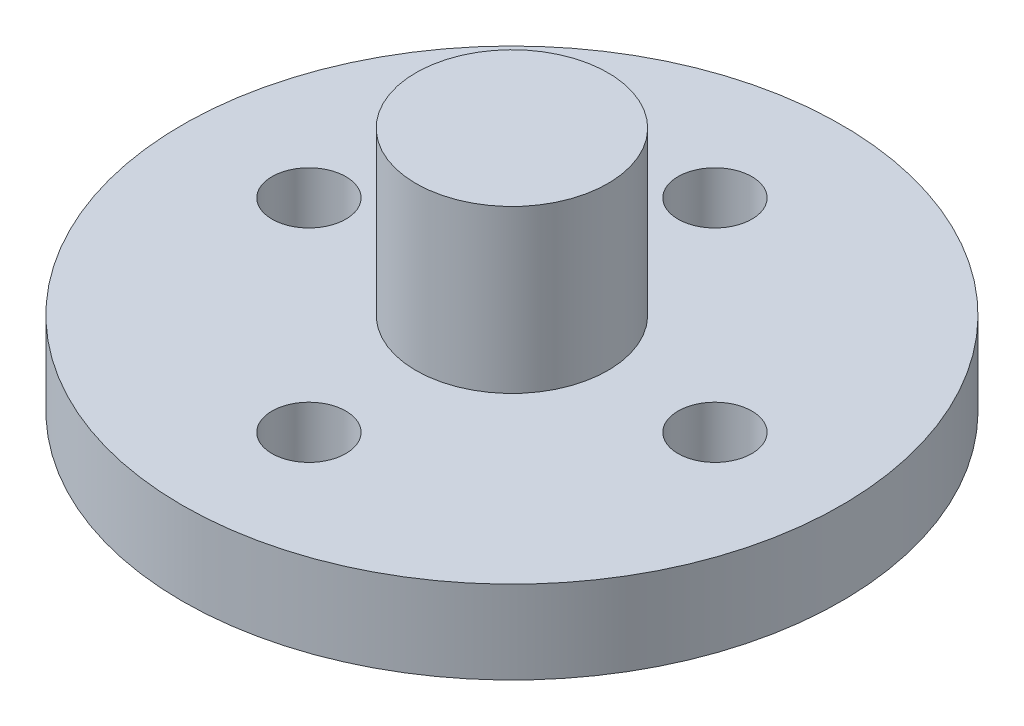
SolidWorks part; units mm, degrees
ref_plane "Front Plane" through (0, 0, 0) normal (0, 0, 1) x (1, 0, 0)
ref_plane "Top Plane" through (0, 0, 0) normal (0, 1, 0) x (1, 0, 0)
ref_plane "Right Plane" through (0, 0, 0) normal (1, 0, 0) x (0, 0, -1)
sketch "Sketch1" plane through (0, 0, 0) normal (0, 1, 0) x (1, 0, 0)
  line L0 (0, 15.5) -> (0, -15.5) construction
  line L1 (-15.5, 0) -> (15.5, 0) construction
  line L2 (-2.4674, 13.4022) -> (-4, 4) construction
  line L3 (4, -4) -> (-4, -4) construction
  line L4 (4, -4) -> (4, 4) construction
  line L5 (4, 4) -> (-4, 4) construction
  line L6 (-4, -4) -> (-4, 4) construction
  line L7 (4, -4) -> (-4, 4) construction
  line L8 (4, 4) -> (-4, -4) construction
  line L9 (-4, 4) -> (-2.4674, 13.4022)
  line L10 (4, 4) -> (2.4674, 13.4022)
  line L11 (4, -4) -> (2.4674, -13.4022)
  line L12 (-4, -4) -> (-2.4674, -13.4022)
  line L13 (-4, 4) -> (-12.5927, 2.4331) construction
  line L14 (-4, 4) -> (-12.4485, 2.4594)
  line L15 (-4, -4) -> (-12.4485, -2.4594)
  line L16 (4, -4) -> (12.4485, -2.4594)
  line L17 (4, 4) -> (12.4485, 2.4594)
  circle A0 centre (0, 0) radius 15.5 construction
  circle A1 centre (0, 0) radius 14.5 construction
  arc A2 (2.4674, 13.4022) -> (-2.4674, 13.4022) centre (0, 13) ccw
  arc A3 (2.4674, -13.4022) -> (-2.4674, -13.4022) centre (0, -13) cw
  arc A4 (-12.4485, 2.4594) -> (-12.4485, -2.4594) centre (-12, 0) ccw
  arc A5 (12.4485, 2.4594) -> (12.4485, -2.4594) centre (12, 0) cw
  circle A6 centre (0, 0) radius 12 construction
  circle A7 centre (0, 0) radius 9.5 construction
  circle A8 centre (0, 0) radius 7.5 construction
  circle A9 centre (0, 12) radius 0.5
  circle A10 centre (0, 9.5) radius 0.5
  circle A11 centre (0, 7.5) radius 0.5
  circle A12 centre (12, 0) radius 0.5
  circle A13 centre (9.5, 0) radius 0.5
  circle A14 centre (7.5, 0) radius 0.5
  circle A15 centre (0, -12) radius 0.5
  circle A16 centre (0, -9.5) radius 0.5
  circle A17 centre (0, -7.5) radius 0.5
  circle A18 centre (-12, 0) radius 0.5
  circle A19 centre (-9.5, 0) radius 0.5
  circle A20 centre (-7.5, 0) radius 0.5
  circle A21 centre (0, 0) radius 1.375
  point P59 (0, 0)
  dimension "D1" = 31
  dimension "D2" = 1
  dimension "D3" = 5
  dimension "D4" = 5
  dimension "D5" = 8
  dimension "D6" = 8
  dimension "D7" = 15
  dimension "D9" = 24
  dimension "D11" = 1
  dimension "D12" = 1
  dimension "D13" = 4
  dimension "D8" = 19
  dimension "D10" = 1
  dimension "D14" = 2.75
extrude "Boss-Extrude1" add sketch "Sketch1" along normal blind 2
sketch "Sketch4" plane through (0, 0, 0) normal (0, -1, 0) x (1, 0, 0)
  circle A0 centre (0, 0) radius 4.627
  circle A1 centre (0, 0) radius 2.627
  dimension "D1" = 9.254
  dimension "D2" = 2
extrude "Boss-Extrude3" add sketch "Sketch4" along normal blind 6.5
sketch "Sketch5" plane through (0, -6.5, 0) normal (0, -1, 0) x (1, 0, 0)
  line L0 (0, 0) -> (0, 0.6245) construction
  line L1 (0, 3.1016) -> (-0.2828, 2.6117)
  line L2 (0, 3.1016) -> (0.2828, 2.6117)
  line L3 (0.9584, 2.9498) -> (0.5381, 2.5713)
  line L4 (0.9584, 2.9498) -> (1.076, 2.3965)
  line L5 (1.8231, 2.5092) -> (1.3063, 2.2792)
  line L6 (1.8231, 2.5092) -> (1.7639, 1.9467)
  line L7 (2.5092, 1.8231) -> (1.9467, 1.7639)
  line L8 (2.5092, 1.8231) -> (2.2792, 1.3063)
  line L9 (2.9498, 0.9584) -> (2.3965, 1.076)
  line L10 (2.9498, 0.9584) -> (2.5713, 0.5381)
  line L11 (3.1016, 0) -> (2.6117, 0.2828)
  line L12 (3.1016, 0) -> (2.6117, -0.2828)
  line L13 (2.9498, -0.9584) -> (2.5713, -0.5381)
  line L14 (2.9498, -0.9584) -> (2.3965, -1.076)
  line L15 (2.5092, -1.8231) -> (2.2792, -1.3063)
  line L16 (2.5092, -1.8231) -> (1.9467, -1.7639)
  line L17 (1.8231, -2.5092) -> (1.7639, -1.9467)
  line L18 (1.8231, -2.5092) -> (1.3063, -2.2792)
  line L19 (0.9584, -2.9498) -> (1.076, -2.3965)
  line L20 (0.9584, -2.9498) -> (0.5381, -2.5713)
  line L21 (0, -3.1016) -> (0.2828, -2.6117)
  line L22 (0, -3.1016) -> (-0.2828, -2.6117)
  line L23 (-0.9584, -2.9498) -> (-0.5381, -2.5713)
  line L24 (-0.9584, -2.9498) -> (-1.076, -2.3965)
  line L25 (-1.8231, -2.5092) -> (-1.3063, -2.2792)
  line L26 (-1.8231, -2.5092) -> (-1.7639, -1.9467)
  line L27 (-2.5092, -1.8231) -> (-1.9467, -1.7639)
  line L28 (-2.5092, -1.8231) -> (-2.2792, -1.3063)
  line L29 (-2.9498, -0.9584) -> (-2.3965, -1.076)
  line L30 (-2.9498, -0.9584) -> (-2.5713, -0.5381)
  line L31 (-3.1016, 0) -> (-2.6117, -0.2828)
  line L32 (-3.1016, 0) -> (-2.6117, 0.2828)
  line L33 (-2.9498, 0.9584) -> (-2.5713, 0.5381)
  line L34 (-2.9498, 0.9584) -> (-2.3965, 1.076)
  line L35 (-2.5092, 1.8231) -> (-2.2792, 1.3063)
  line L36 (-2.5092, 1.8231) -> (-1.9467, 1.7639)
  line L37 (-1.8231, 2.5092) -> (-1.7639, 1.9467)
  line L38 (-1.8231, 2.5092) -> (-1.3063, 2.2792)
  line L39 (-0.9584, 2.9498) -> (-1.076, 2.3965)
  line L40 (-0.9584, 2.9498) -> (-0.5381, 2.5713)
  circle A0 centre (0, 0) radius 2.627 construction
  arc A1 (-2.2792, 1.3063) -> (-2.3965, 1.076) centre (0, 0) ccw
  arc A2 (-1.7639, 1.9467) -> (-1.9467, 1.7639) centre (0, 0) ccw
  arc A3 (-1.076, 2.3965) -> (-1.3063, 2.2792) centre (0, 0) ccw
  arc A4 (-0.2828, 2.6117) -> (-0.5381, 2.5713) centre (0, 0) ccw
  arc A5 (0.5381, 2.5713) -> (0.2828, 2.6117) centre (0, 0) ccw
  arc A6 (1.3063, 2.2792) -> (1.076, 2.3965) centre (0, 0) ccw
  arc A7 (1.9467, 1.7639) -> (1.7639, 1.9467) centre (0, 0) ccw
  arc A8 (2.3965, 1.076) -> (2.2792, 1.3063) centre (0, 0) ccw
  arc A9 (2.6117, 0.2828) -> (2.5713, 0.5381) centre (0, 0) ccw
  arc A10 (2.5713, -0.5381) -> (2.6117, -0.2828) centre (0, 0) ccw
  arc A11 (2.2792, -1.3063) -> (2.3965, -1.076) centre (0, 0) ccw
  arc A12 (1.7639, -1.9467) -> (1.9467, -1.7639) centre (0, 0) ccw
  arc A13 (1.076, -2.3965) -> (1.3063, -2.2792) centre (0, 0) ccw
  arc A14 (0.2828, -2.6117) -> (0.5381, -2.5713) centre (0, 0) ccw
  arc A15 (-0.5381, -2.5713) -> (0, -2.627) centre (0, 0) ccw
  arc A16 (-1.3063, -2.2792) -> (-1.076, -2.3965) centre (0, 0) ccw
  arc A17 (-1.9467, -1.7639) -> (-1.7639, -1.9467) centre (0, 0) ccw
  arc A18 (-2.3965, -1.076) -> (-2.2792, -1.3063) centre (0, 0) ccw
  arc A19 (-2.6117, -0.2828) -> (-2.5713, -0.5381) centre (0, 0) ccw
  arc A20 (-2.5713, 0.5381) -> (-2.6117, 0.2828) centre (0, 0) ccw
  point P68 (0, 0)
  circle M5 centre (0, 0) radius 2.627
  dimension "D1" = 30
  dimension "D2" = 3.1016
  dimension "D3" = 20
extrude "Cut-Extrude3" cut sketch "Sketch5" against normal up to surface (6.5 mm away) contours L36 L35 M5 | L34 L33 M5 | L32 L31 M5 | L30 L29 M5 | L28 L27 M5 | L26 L25 M5 | L24 L23 M5 | L0 L21 M5 | L22 L0 M5 | L20 L19 M5 | L18 L17 M5 | L16 L15 M5 | L14 L13 M5 | L12 L11 M5 | L10 L9 M5 | L8 L7 M5 | L6 L5 M5 | L4 L3 M5 | L0 L2 M5 | L0 L1 M5 | L40 L39 M5 | L38 L37 M5
sketch "Sketch6" plane through (0, 2, 0) normal (0, 1, 0) x (1, 0, 0)
  circle A0 centre (0, 0) radius 15.875
  circle A2 centre (0, 0) radius 3.75
  dimension "D1" = 31.75
extrude "Boss-Extrude6" add sketch "Sketch6" against normal blind 2.54
sketch "Sketch7" plane through (0, 2, 0) normal (0, 1, 0) x (1, 0, 0)
  circle A0 centre (0, 9.779) radius 1.778
extrude "Cut-Extrude4" cut sketch "Sketch7" against normal blind 2.54
pattern_circular "CirPattern1" count 4 over 360 about axis through (0, 0, 0) along (0, 1, 0) of "Cut-Extrude4"
sketch "Esquisse1" plane through (0, 2, 0) normal (0, 1, 0) x (1, 0, 0)
  circle A0 centre (0, 0) radius 15.875
  circle A1 centre (0, 0) radius 1.375
  circle A2 centre (0, 9.779) radius 1.778
  circle A3 centre (9.779, 0) radius 1.778
  circle A4 centre (0, -9.779) radius 1.778
  circle A5 centre (-9.779, 0) radius 1.778
extrude "Boss.-Extru.1" add sketch "Esquisse1" along normal blind 1.46
sketch "Esquisse2" plane through (0, 3.46, 0) normal (0, 1, 0) x (1, 0, 0)
  circle A0 centre (0, 0) radius 4.625
  dimension "D1" = 9.25
extrude "Boss.-Extru.2" add sketch "Esquisse2" along normal blind 7.8
